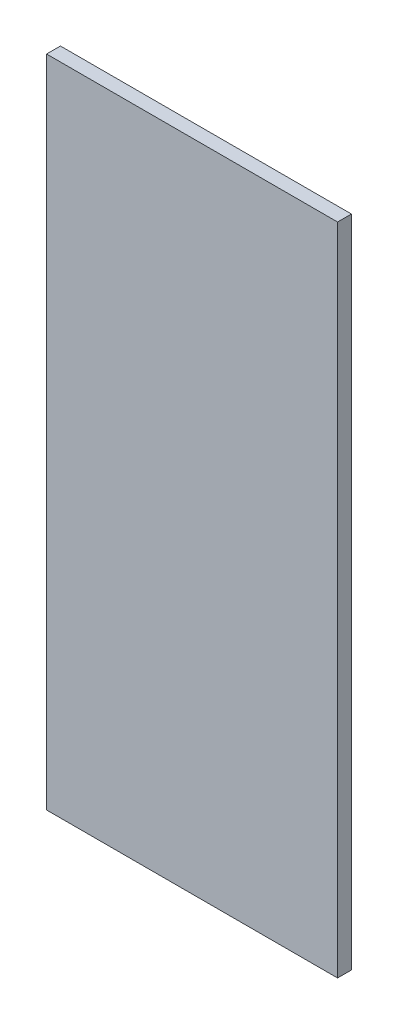
SolidWorks part; units mm, degrees
ref_plane "Front Plane" through (0, 0, 0) normal (0, 0, 1) x (1, 0, 0)
ref_plane "Top Plane" through (0, 0, 0) normal (0, 1, 0) x (1, 0, 0)
ref_plane "Right Plane" through (0, 0, 0) normal (1, 0, 0) x (0, 0, -1)
sketch "Sketch1" plane through (0, 0, 0) normal (0, 0, 1) x (1, 0, 0)
  line L1 (0, 0) -> (400, 0)
  line L2 (0, 0) -> (0, -900)
  line L3 (0, -900) -> (400, -900)
  line L4 (400, 0) -> (400, -900)
  dimension "D1" = 400
  dimension "D2" = 900
extrude "Boss-Extrude1" add sketch "Sketch1" along normal blind 19.05
